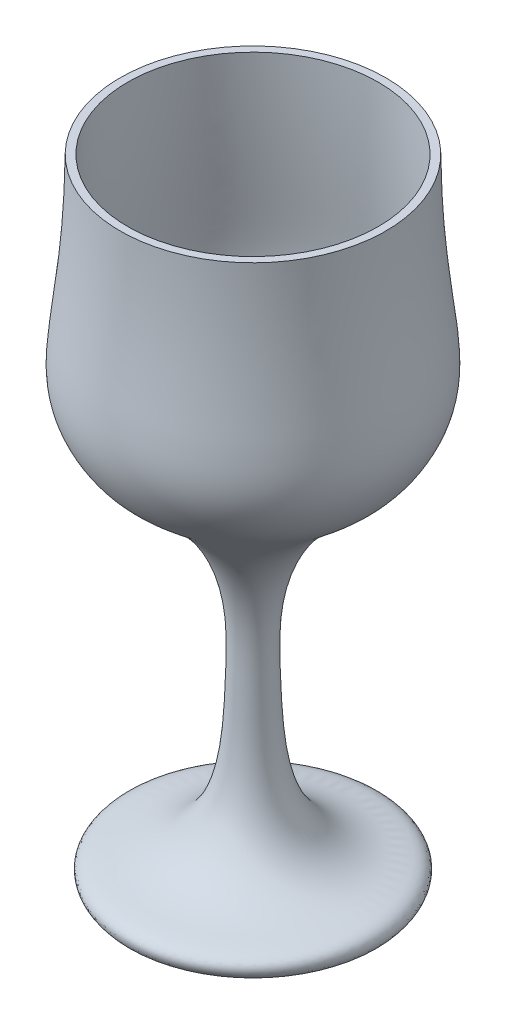
SolidWorks part; units mm, degrees
ref_plane "Face" through (0, 0, 0) normal (0, 0, 1) x (1, 0, 0)
ref_plane "Dessus" through (0, 0, 0) normal (0, 1, 0) x (1, 0, 0)
ref_plane "Droite" through (0, 0, 0) normal (1, 0, 0) x (0, 0, -1)
sketch "Esquisse1" plane through (0, 0, 0) normal (0, 0, 1) x (1, 0, 0)
  line L0 (0, 0) -> (0, 165) construction
  line L1 (0, 0) -> (32.5, 0)
  line L3 (0, 165) -> (35, 165) construction
  line L5 (35, 165) -> (33, 165)
  line L6 (34, 165) -> (34, 166.3627) construction
  line L7 (0, 77.0201) -> (0, 0)
  spline S0 degree 3 poles (32.5, 0) (33.5896, 1.3531) (33.1376, 4.5874) (7.2558, 6.6373) (5.4797, 31.5582) (4.0689, 81.7964) (27.7426, 92.0918) (43.5052, 116.8261) (35.4367, 126.1625) (35, 165) knots 0 0 0 0 0.012064 0.033714 0.196193 0.247333 0.493982 0.572332 1 1 1 1
  spline S1 degree 3 poles (0, 77.0201) (6.2858, 78.1851) (27.9848, 95.2408) (39.776, 114.8987) (33.4367, 126.1625) (33, 165) knots 0.29921 0.29921 0.29921 0.29921 0.502253 0.572332 1 1 1 1
  dimension "D1" = 165
  dimension "D2" = 32.5
  dimension "D3" = 5
revolve "Révolution1" add sketch "Esquisse1" angle 360 about L0
